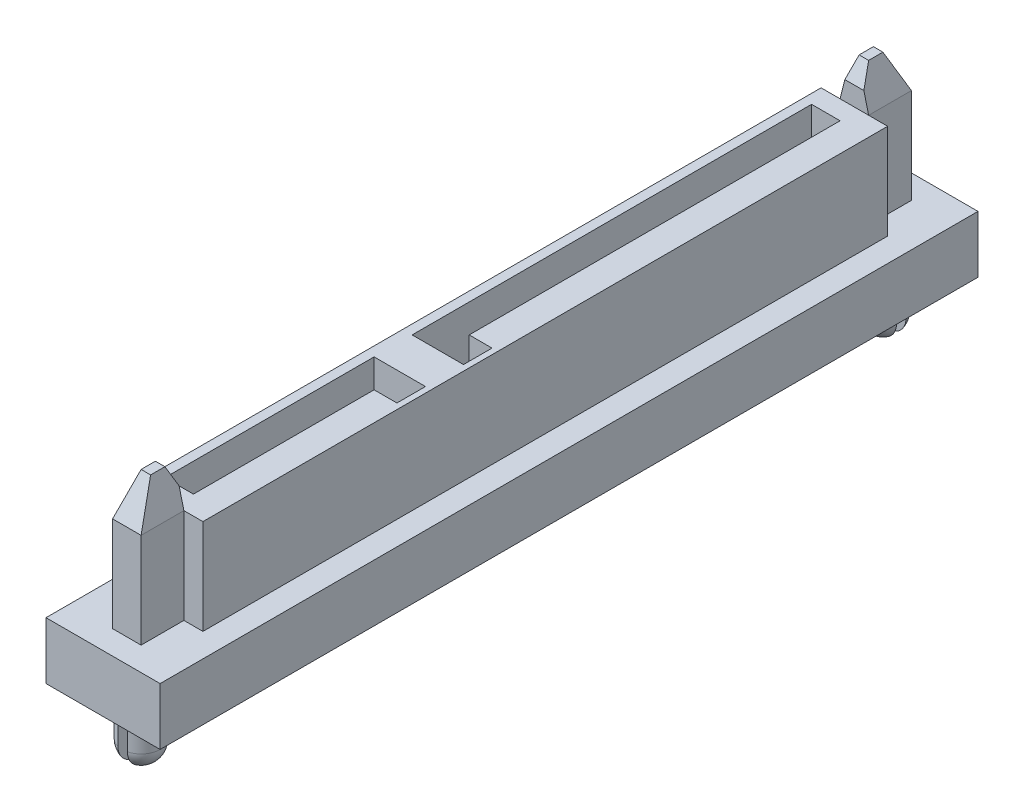
SolidWorks part; units mm, degrees
ref_plane "前视基准面" through (0, 0, 0) normal (0, 0, 1) x (1, 0, 0)
ref_plane "上视基准面" through (0, 0, 0) normal (0, 1, 0) x (1, 0, 0)
ref_plane "右视基准面" through (0, 0, 0) normal (1, 0, 0) x (0, 0, -1)
sketch "草图1" plane through (0, 0, 0) normal (0, 1, 0) x (1, 0, 0)
  line L1 (3, 21.5) -> (-3, 21.5)
  line L2 (3, 21.5) -> (3, -21.5)
  line L3 (3, -21.5) -> (-3, -21.5)
  line L4 (-3, 21.5) -> (-3, -21.5)
  line L5 (3, 21.5) -> (-3, -21.5) construction
  line L6 (3, -21.5) -> (-3, 21.5) construction
  point P0 (0, 0)
  dimension "D1" = 43
  dimension "D2" = 6
extrude "凸台-拉伸1" add sketch "草图1" along normal blind 10
sketch "草图3" plane through (0, 0, 0) normal (0, -1, 0) x (1, 0, 0)
  line L0 (0, 0) -> (-7.9648, 0) construction
  line L1 (-7.9648, 0) -> (0, 0) construction
  line L2 (0, 0) -> (0, 7.59) construction
  circle A0 centre (0, 19.5) radius 1
  circle A1 centre (0, -19.5) radius 1
  dimension "D2" = 2
  dimension "D1" = 39
extrude "凸台-拉伸2" add sketch "草图3" along normal blind 3
fillet "圆角1" radius 1 2 edges at (0, -3, 18.5) (0, -3, -20.5)
sketch "草图4" plane through (0, 0, 0) normal (0, -1, 0) x (1, 0, 0)
  line L1 (0.25, 18.5) -> (-0.25, 18.5)
  line L2 (0.25, 18.5) -> (0.25, 20.5)
  line L3 (0.25, 20.5) -> (-0.25, 20.5)
  line L4 (-0.25, 18.5) -> (-0.25, 20.5)
  line L5 (0.25, 18.5) -> (-0.25, 20.5) construction
  line L6 (0.25, 20.5) -> (-0.25, 18.5) construction
  line L7 (1, -19.25) -> (-1, -19.25)
  line L8 (1, -19.25) -> (1, -19.75)
  line L9 (1, -19.75) -> (-1, -19.75)
  line L10 (-1, -19.25) -> (-1, -19.75)
  line L11 (1, -19.25) -> (-1, -19.75) construction
  line L12 (1, -19.75) -> (-1, -19.25) construction
  circle A0 centre (0, -19.5) radius 1 construction
  circle A1 centre (0, 19.5) radius 1 construction
  point P0 (0, 19.5)
  point P6 (0, -19.5)
  dimension "D1" = 0.5
  dimension "D2" = 0.5
extrude "切除-拉伸1" cut sketch "草图4" along normal through all
sketch "草图5" plane through (0, 10, 0) normal (0, 1, 0) x (1, 0, 0)
  line L0 (0, 0) -> (3.7701, 0) construction
  line L1 (-0.75, -20.25) -> (0.75, -20.25)
  line L2 (-1.75, -18) -> (-1.75, 18)
  line L3 (-0.75, 20.25) -> (0.75, 20.25)
  line L4 (1.75, -18) -> (1.75, 18)
  line L9 (1.75, 18) -> (0.75, 18)
  line L10 (0.75, 20.25) -> (0.75, 18)
  line L13 (-1.75, 18) -> (-0.75, 18)
  line L14 (-0.75, 20.25) -> (-0.75, 18)
  line L17 (-1.75, -18) -> (-0.75, -18)
  line L18 (-0.75, -20.25) -> (-0.75, -18)
  line L21 (1.75, -18) -> (0.75, -18)
  line L22 (0.75, -20.25) -> (0.75, -18)
  line L23 (0, 0) -> (0, 7.2198) construction
  point P0 (0, 0)
  dimension "D1" = 40.5
  dimension "D2" = 3.5
  dimension "D3" = 1.5
  dimension "D4" = 36
extrude "切除-拉伸2" cut sketch "草图5" against normal blind 7 flip side to cut
sketch "草图6" plane through (0, 10, 0) normal (0, 1, 0) x (1, 0, 0)
  line L0 (-0.75, 18) -> (-1.75, 18) construction
  line L1 (-1.25, 17) -> (0.25, 17)
  line L2 (-1.25, 17) -> (-1.25, -4)
  line L3 (-1.25, -4) -> (1.45, -4)
  line L4 (0.25, 17) -> (0.25, -2.5)
  line L7 (0.25, -2.5) -> (1.45, -2.5)
  line L8 (1.45, -4) -> (1.45, -2.5)
  line L9 (-1.25, -17) -> (0.25, -17)
  line L10 (-1.25, -17) -> (-1.25, -6)
  line L11 (-1.25, -6) -> (1.45, -6)
  line L12 (0.25, -17) -> (0.25, -7.5)
  line L15 (0.25, -7.5) -> (1.45, -7.5)
  line L16 (1.45, -6) -> (1.45, -7.5)
  line L17 (-1.75, 18) -> (-1.75, -18) construction
  line L18 (1.75, -18) -> (1.75, 18) construction
  line L19 (-1.75, -18) -> (-0.75, -18) construction
  dimension "D1" = 1
  dimension "D2" = 0.5
  dimension "D3" = 1.5
  dimension "D4" = 21
  dimension "D5" = 0.3
  dimension "D6" = 1
  dimension "D7" = 2
extrude "切除-拉伸3" cut sketch "草图6" against normal blind 7
sketch "草图7" plane through (0, 10, 0) normal (0, 1, 0) x (1, 0, 0)
  line L0 (1.75, -18) -> (1.75, 18) construction
  line L1 (-1.75, 18) -> (1.75, 18)
  line L2 (-1.75, 18) -> (-1.75, -18)
  line L3 (-1.75, -18) -> (1.75, -18)
  line L4 (1.75, 18) -> (1.75, -18)
  line L5 (-1.75, 18) -> (1.75, -18) construction
  line L6 (-1.75, -18) -> (1.75, 18) construction
  line L7 (1.75, 18) -> (0.75, 18) construction
  point P0 (0, 0)
extrude "切除-拉伸4" cut sketch "草图7" against normal blind 2
chamfer "倒角1" distance 2 distance2 0.5 3 edges at (0.75, 10, -19.125) (0, 10, -20.25) (-0.75, 10, -19.125)
chamfer "倒角2" distance 2 distance2 0.5 3 edges at (0.75, 10, 19.125) (0, 10, 20.25) (-0.75, 10, 19.125)
chamfer "倒角3" distance 2 distance2 1 2 edges at (0, 10, -20.25) (0, 10, 20.25)
chamfer "倒角4" distance 0.5 distance2 1 2 edges at (0, 10, 18) (0, 10, -18)
